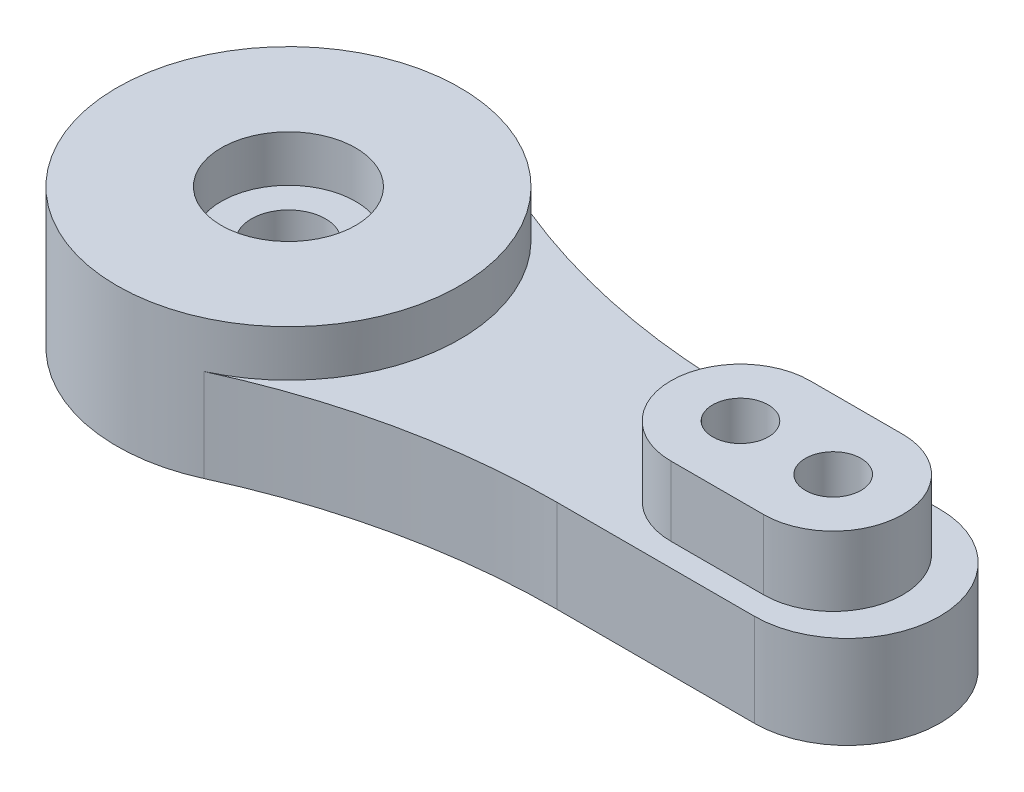
SolidWorks part; units mm, degrees
ref_plane "Front" through (0, 0, 0) normal (0, 0, 1) x (1, 0, 0)
ref_plane "Top" through (0, 0, 0) normal (0, 1, 0) x (1, 0, 0)
ref_plane "Right" through (0, 0, 0) normal (1, 0, 0) x (0, 0, -1)
sketch "Sketch1" plane through (0, 0, 0) normal (0, 1, 0) x (1, 0, 0)
  line L0 (0, 0) -> (34.693, 0) construction
  line L1 (0, 0) -> (24.1, 0) construction
  line L2 (0, 4) -> (24.1, 4)
  line L3 (0, -4) -> (24.1, -4)
  line L4 (0, 0) -> (-7.4, 0) construction
  circle A0 centre (0, 0) radius 7.4
  circle A1 centre (19.5, 0) radius 1.2
  circle A2 centre (23.5, 0) radius 1.2
  arc A3 (0, 4) -> (0, -4) centre (0, 0) ccw
  arc A4 (24.1, -4) -> (24.1, 4) centre (24.1, 0) ccw
  arc A5 (3.0828, 6.7273) -> (15.5808, 4) centre (15.5808, 34) ccw
  arc A6 (3.0828, -6.7273) -> (15.5808, -4) centre (15.5808, -34) cw
  circle A7 centre (0, 0) radius 1.6
  point P8 (12.05, 0)
  point P14 (28.1, 0)
  dimension "D3" = 14.8
  dimension "D4" = 4
  dimension "D6" = 30
  dimension "D7" = 2.4
  dimension "D8" = 2.4
  dimension "D9" = 3.2
  dimension "D1" = 19.5
  dimension "D2" = 23.5
  dimension "D5" = 35.5
extrude "Boss-Extrude1" add sketch "Sketch1" along normal blind 4 contours A3 L2 A0 L3 | A7 L3 A0 L2 | A5 A0 L2 | A0 A6 L3 | L3 A4 L2 A0 A1 A2
sketch "Sketch2" plane through (0, 4, 0) normal (0, 1, 0) x (1, 0, 0)
  line L0 (19.5, 0) -> (23.5, 0) construction
  line L1 (19.5, 3) -> (23.5, 3)
  line L2 (19.5, -3) -> (23.5, -3)
  arc A0 (19.5, 3) -> (19.5, -3) centre (19.5, 0) ccw
  arc A1 (23.5, -3) -> (23.5, 3) centre (23.5, 0) ccw
  circle A2 centre (19.5, 0) radius 1.2 construction
  circle A3 centre (23.5, 0) radius 1.2 construction
  circle A4 centre (19.5, 0) radius 1.2
  circle A5 centre (23.5, 0) radius 1.2
  point P4 (21.5, 0)
  dimension "D1" = 3
extrude "Boss-Extrude2" add sketch "Sketch2" along normal blind 3
sketch "Sketch3" plane through (0, 4, 0) normal (0, 1, 0) x (1, 0, 0)
  circle A0 centre (0, 0) radius 2.9
  arc A2 (3.0828, 6.7273) -> (3.0828, -6.7273) centre (0, 0) ccw construction
  arc A3 (3.0828, 6.7273) -> (3.0828, -6.7273) centre (0, 0) ccw
  circle A4 centre (0, 0) radius 7.4
  arc M10 (3.0828, 6.7273) -> (3.0828, -6.7273) centre (0, 0) ccw
  dimension "D1" = 5.8
extrude "Boss-Extrude3" add sketch "Sketch3" along normal blind 2 contours A4 A0 M10
